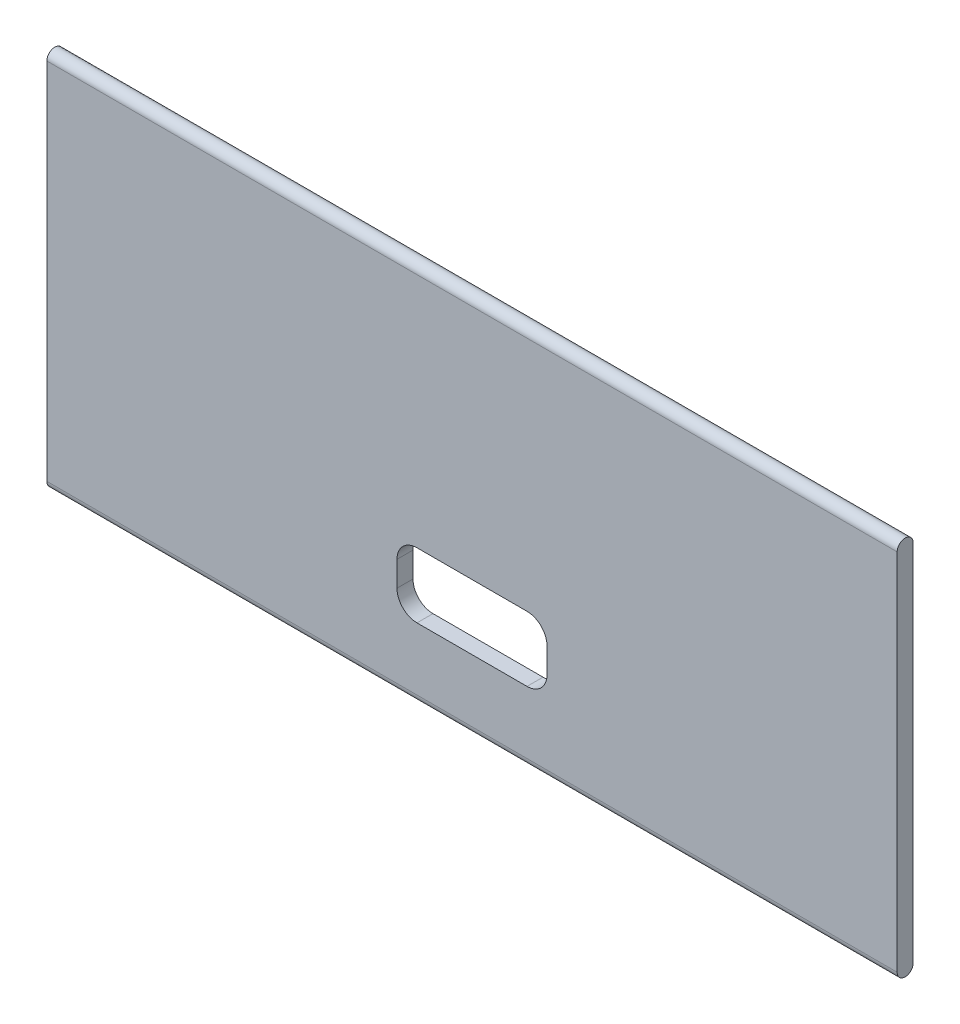
SolidWorks part; units mm, degrees
ref_plane "Front Plane" through (0, 0, 0) normal (0, 0, 1) x (1, 0, 0)
ref_plane "Top Plane" through (0, 0, 0) normal (0, 1, 0) x (1, 0, 0)
ref_plane "Right Plane" through (0, 0, 0) normal (1, 0, 0) x (0, 0, -1)
sketch "Sketch1" plane through (0, 0, 0) normal (1, 0, 0) x (0, 0, -1)
  line L0 (0.8, 17.2085) -> (0.8, -18.2028)
  line L1 (-0.8, 18.1972) -> (-0.8, -18.1915)
  line L2 (-0.8, 18.1972) -> (0.8, 18.1972) construction
  line L3 (0.8, 17.2085) -> (0.8, 18.1972)
  arc A0 (0.8, -18.2028) -> (-0.8, -18.1915) centre (0, -18.1972) cw
  arc A1 (0.8, 18.1972) -> (-0.8, 18.1972) centre (0, 18.1972) ccw
  point P0 (-0.1178, -1.2915)
extrude "Boss-Extrude1" add sketch "Sketch1" along normal blind 85
sketch "Sketch2" plane through (0, 0, 0.8) normal (0, 0, 1) x (1, 0, 0)
  line L0 (42.5, 19.753) -> (42.5, -18.247) construction
  line L1 (37, -5.4472) -> (48, -5.4472)
  line L2 (35, -7.4472) -> (35, -9.9472)
  line L3 (37, -11.9472) -> (48, -11.9472)
  line L4 (50, -7.4472) -> (50, -9.9472)
  line L5 (35, -5.4472) -> (50, -11.9472) construction
  line L6 (35, -11.9472) -> (50, -5.4472) construction
  line L7 (0, 18.1972) -> (85, 18.1972) construction
  line L8 (85, -18.1972) -> (0, -18.1972) construction
  arc A0 (37, -5.4472) -> (35, -7.4472) centre (37, -7.4472) ccw
  arc A1 (35, -9.9472) -> (37, -11.9472) centre (37, -9.9472) ccw
  arc A2 (48, -11.9472) -> (50, -9.9472) centre (48, -9.9472) ccw
  arc A3 (48, -5.4472) -> (50, -7.4472) centre (48, -7.4472) cw
  point P2 (42.5, -8.6972)
  point P23 (42.5, 18.1972)
  dimension "D1" = 15
  dimension "D2" = 6.5
  dimension "D3" = 6.25
extrude "Cut-Extrude1" cut sketch "Sketch2" against normal up to next
